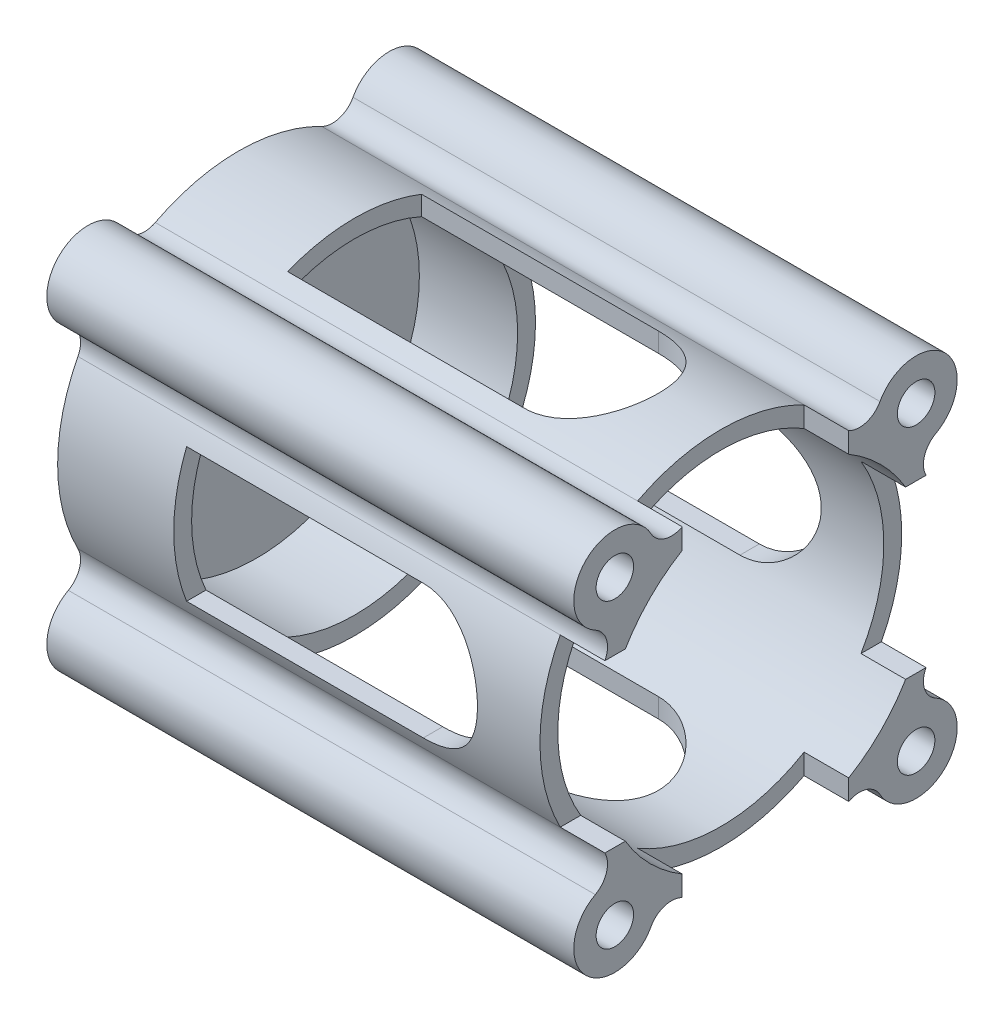
SolidWorks part; units mm, degrees
material "ABS"
ref_plane "Спереди" through (0, 0, 0) normal (0, 0, 1) x (1, 0, 0)
ref_plane "Сверху" through (0, 0, 0) normal (0, 1, 0) x (1, 0, 0)
ref_plane "Справа" through (0, 0, 0) normal (1, 0, 0) x (0, 0, -1)
sketch "Эскиз1" plane through (0, 0, 0) normal (1, 0, 0) x (0, 0, -1)
  circle A0 centre (0, 0) radius 20.25
  dimension "D1" = 40.5
extrude "Бобышка-Вытянуть1" add sketch "Эскиз1" along normal blind 2
sketch "Эскиз2" plane through (0, 0, 0) normal (-1, 0, 0) x (0, 0, 1)
  circle A0 centre (0, 0) radius 3.5
  dimension "D1" = 7
extrude "Вырез-Вытянуть1" cut sketch "Эскиз2" against normal through all
sketch "Эскиз3" plane through (2, 0, 0) normal (1, 0, 0) x (0, 0, -1)
  circle A0 centre (0, 0) radius 10.25
  circle A1 centre (0, 0) radius 20.25
  circle A2 centre (0, 0) radius 20.25 construction
  dimension "D1" = 20.5
extrude "Бобышка-Вытянуть2" add sketch "Эскиз3" along normal blind 4.1
sketch "Эскиз5" plane through (6.1, 0, 0) normal (1, 0, 0) x (0, 0, -1)
  circle A0 centre (0, 0) radius 16.25
  circle A1 centre (0, 0) radius 20.25
  circle A2 centre (0, 0) radius 20.25 construction
  dimension "D2" = 32.5
extrude "Бобышка-Вытянуть3" add sketch "Эскиз5" along normal blind 5.4
sketch "Эскиз6" plane through (11.5, 0, 0) normal (1, 0, 0) x (0, 0, -1)
  circle A0 centre (0, 0) radius 18.25
  circle A1 centre (0, 0) radius 20.25
  circle A2 centre (0, 0) radius 20.25 construction
  dimension "D2" = 36.5
extrude "Бобышка-Вытянуть4" add sketch "Эскиз6" along normal blind 47.5
sketch "Эскиз7" plane through (0, 0, 0) normal (-1, 0, 0) x (0, 0, 1)
  line L0 (0, 0) -> (-14.3189, -14.3189) construction
  line L1 (-14.3189, -14.3189) -> (14.3189, 14.3189) construction
  line L2 (0, 0) -> (-14.3189, 14.3189) construction
  line L3 (-14.3189, 14.3189) -> (14.3189, -14.3189) construction
  circle A0 centre (0, 0) radius 20.25 construction
  circle A1 centre (-9.1924, 9.1924) radius 1.5
  dimension "D1" = 13
  dimension "D2" = 3
extrude "Вырез-Вытянуть2" cut sketch "Эскиз7" against normal through all
pattern_circular "Круговой массив1" count 4 over 360 about axis through (0, 0, 0) along (1, 0, 0) of "Вырез-Вытянуть2"
fillet "Скругление1" radius 0.5 5 edges at (6.1, 0, -10.25) (11.5, 0, -16.25) (6.1, 0, -16.25) (11.5, 0, -18.25) (2, 0, -10.25)
sketch "Эскиз9" plane through (0, 0, 0) normal (-1, 0, 0) x (0, 0, 1)
  line L0 (-21.4838, 21.4838) -> (21.4838, -21.4838) construction
  line L1 (21.4838, 21.4838) -> (-21.4838, -21.4838) construction
  line L2 (0, 0) -> (0, 20.25) construction
  circle A0 centre (0, 0) radius 20.25 construction
  circle A1 centre (-16.8645, 16.8645) radius 2.1
  circle A2 centre (-16.8645, 16.8645) radius 4.6
  point P4 (0, 0)
  point P6 (0, 0)
  point P27 (0, 0)
  dimension "D3" = 4.2
  dimension "D4" = 9.2
  dimension "D1" = 45
  dimension "D2" = 45
  dimension "D5" = 23.85
extrude "Бобышка-Вытянуть6" add sketch "Эскиз9" against normal up to surface (59 mm away) up to face at (59, 0, -20.25)
sketch "Эскиз10" plane through (0, 0, 0) normal (-1, 0, 0) x (0, 0, 1)
  line L0 (-16.8645, 16.8645) -> (-9.1924, 9.1924) construction
  arc A0 (-12.8187, 19.0535) -> (-9.32, 17.9778) centre (-10.5219, 20.2961) ccw
  arc A1 (-9.32, 17.9778) -> (-12.3355, 16.0592) centre (0, 0) ccw
  arc A2 (-16.0592, 12.3355) -> (-12.3355, 16.0592) centre (0, 0) ccw construction
  arc A3 (-19.0535, 12.8187) -> (-12.8187, 19.0535) centre (-16.8645, 16.8645) ccw
  arc A4 (-12.3355, 16.0592) -> (-16.0592, 12.3355) centre (-16.8645, 16.8645) ccw construction
  arc A5 (-19.0535, 12.8187) -> (-17.9778, 9.32) centre (-20.2961, 10.5219) cw
  arc A6 (-16.0592, 12.3355) -> (-17.9778, 9.32) centre (0, 0) ccw
  arc M15 (-16.0592, 12.3355) -> (-12.3355, 16.0592) centre (0, 0) ccw
  arc M16 (-12.3355, 16.0592) -> (-16.0592, 12.3355) centre (-16.8645, 16.8645) ccw
extrude "Бобышка-Вытянуть7" add sketch "Эскиз10" against normal up to surface (59 mm away) contours A0 M16 M15 | A5 M16 M15
pattern_circular "Круговой массив3" count 4 over 360 about axis through (0, 0, 0) along (1, 0, 0) of "Бобышка-Вытянуть7", "Бобышка-Вытянуть6"
sketch "Эскиз11" plane through (0, 0, 0) normal (0, 1, 0) x (1, 0, 0)
  line L0 (59, -9.32) -> (59, 9.32) construction
  line L1 (13, 7.5) -> (39.5, 7.5)
  line L2 (13, 7.5) -> (13, -7.5)
  line L3 (13, -7.5) -> (39.5, -7.5)
  line L5 (0, 9.32) -> (0, -9.32) construction
  arc A0 (39.5, -7.5) -> (39.5, 7.5) centre (39.5, 0) ccw
  point P1 (47, 0)
  point P7 (59, 0)
  dimension "D1" = 12
  dimension "D2" = 15
  dimension "D3" = 13
extrude "Вырез-Вытянуть3" cut sketch "Эскиз11" against normal through all and the other way through all
pattern_circular "Круговой массив4" count 2 every 270 about axis through (2, 0, 0) along (-1, 0, 0) of "Вырез-Вытянуть3"
sketch "Эскиз22" plane through (2, 0, 0) normal (1, 0, 0) x (0, 0, -1)
  circle A0 centre (0, 0) radius 18.25
  dimension "D1" = 36.5
extrude "Вырез-Вытянуть9" cut sketch "Эскиз22" along normal blind 20
ref_plane "Плоскость1" through (0, -21.4645, 0) normal (0, -1, 0) x (-1, 0, 0)
sketch "Эскиз23" plane through (0, -21.4645, 0) normal (0, -1, 0) x (-1, 0, 0)
  line L0 (-59, 9.32) -> (-59, -9.32) construction
  line L1 (-59, 9.32) -> (-54, 9.32)
  line L2 (-59, 9.32) -> (-59, -9.32)
  line L3 (-59, -9.32) -> (-54, -9.32)
  line L4 (-54, 9.32) -> (-54, -9.32)
  line L5 (-59, -9.32) -> (0, -9.32) construction
  line L6 (-59, 9.32) -> (0, 9.32) construction
  dimension "D1" = 5
extrude "Вырез-Вытянуть10" cut sketch "Эскиз23" against normal through all
pattern_circular "Круговой массив5" count 2 every 270 about axis through (2, 0, 0) along (-1, 0, 0) of "Вырез-Вытянуть10"
sketch "Эскиз25" plane through (0, 0, 0) normal (-1, 0, 0) x (0, 0, 1)
  line L1 (-0.3576, -15.7612) -> (0.6168, -15.7612)
  line L2 (-0.3576, -15.7612) -> (-0.3576, -17.0516)
  line L3 (-0.3576, -17.0516) -> (0.6168, -17.0516)
  line L4 (0.6168, -15.7612) -> (0.6168, -17.0516)
extrude "Бобышка-Вытянуть8" [suppressed] add sketch "Эскиз25" along normal blind 12
